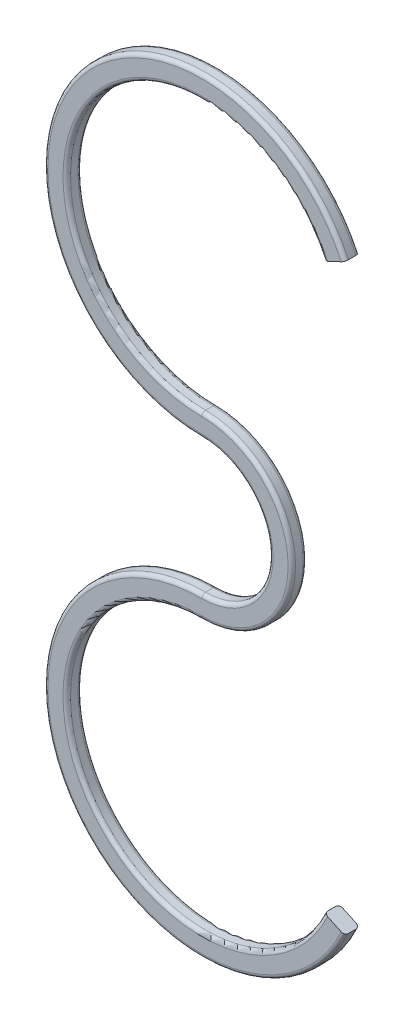
SolidWorks part; units mm, degrees
ref_plane "Front Plane" through (0, 0, 0) normal (0, 0, 1) x (1, 0, 0)
ref_plane "Top Plane" through (0, 0, 0) normal (0, 1, 0) x (1, 0, 0)
ref_plane "Right Plane" through (0, 0, 0) normal (1, 0, 0) x (0, 0, -1)
sketch "Sketch1" plane through (0, 0, 0) normal (0, 0, 1) x (1, 0, 0)
  line L0 (0, 0) -> (0, 15) construction
  line L1 (0, 15) -> (13.5946, 21.3393) construction
  line L2 (7.5, 0) -> (-7.5, 0) construction
  circle A0 centre (0, 15) radius 9 construction
  arc A1 (8.1568, 18.8036) -> (0, 6) centre (0, 15) ccw
  arc A2 (0, 6) -> (6, 0) centre (0, 0) cw
  arc A3 (0, -6) -> (6, 0) centre (0, 0) ccw
  arc A4 (8.1568, -18.8036) -> (0, -6) centre (0, -15) cw
  point P8 (0, 0)
  point P11 (0, 0)
  point P12 (0, 0)
  point P19 (0, 0)
  dimension "D3" = 18
  dimension "D1" = 15
  dimension "D2" = 65
extrude "Extrude-Thin1" add sketch "Sketch1" along normal blind 1 thin
fillet "Fillet1" radius 0.25 12 edges at (-8.8556, 20.6416, 0) (4.5, 0, 0) (6, 0, 0) (6, 0, 1) (-8.8556, 20.6416, 1) (4.5, 0, 1) (-8.8556, -20.6416, 0) (-7.5905, -19.8357, 0) (-7.5905, 19.8357, 1) (-7.5905, 19.8357, 0) (-7.5905, -19.8357, 1) (-8.8556, -20.6416, 1)
